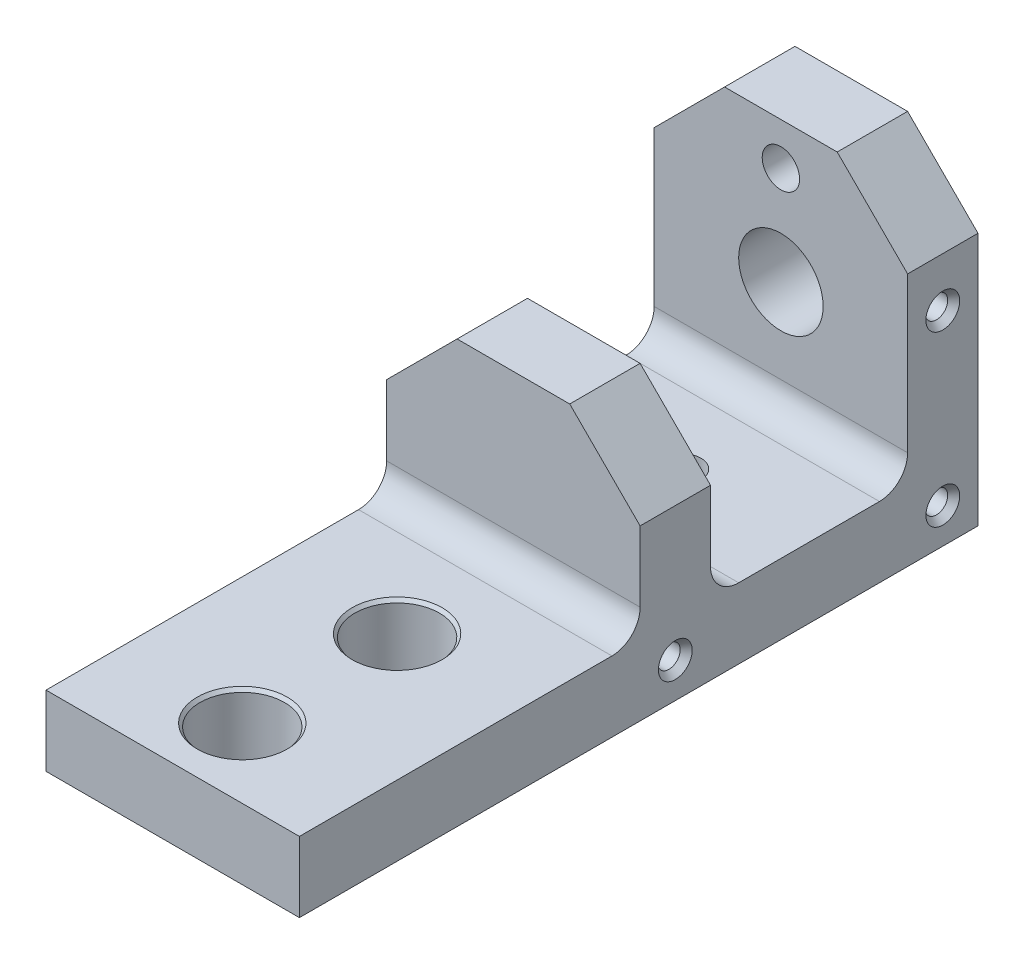
SolidWorks part; units mm, degrees
material "AISI 1018 Steel, Cold Rolled"
ref_plane "Front" through (0, 0, 0) normal (0, 0, 1) x (1, 0, 0)
ref_plane "Top" through (0, 0, 0) normal (0, 1, 0) x (1, 0, 0)
ref_plane "Right" through (0, 0, 0) normal (1, 0, 0) x (0, 0, -1)
sketch "Sketch5" plane through (0, 0, 0) normal (1, 0, 0) x (0, 0, -1)
  line L0 (0, 46.0375) -> (0, -7.9375)
  line L3 (0, -7.9375) -> (-92.71, -7.9375)
  line L4 (-92.71, -7.9375) -> (-92.71, 7.9375)
  line L5 (-92.71, 7.9375) -> (-15.875, 7.9375)
  line L6 (-15.875, 7.9375) -> (-15.875, 46.0375)
  line L7 (-15.875, 46.0375) -> (0, 46.0375)
  line L8 (-92.71, 0) -> (0, 0) construction
  dimension "D1" = 15.875
  dimension "D2" = 76.835
  dimension "D3" = 38.1
extrude "Extrude4" add sketch "Sketch5" along normal blind 57.15
sketch "Sketch9" plane through (57.15, 0, 0) normal (1, 0, 0) x (0, 0, -1)
  line L0 (0, 7.9375) -> (44.45, 7.9375)
  line L1 (44.45, 7.9375) -> (44.45, 65.0875)
  line L2 (44.45, 65.0875) -> (60.325, 65.0875)
  line L3 (60.325, 65.0875) -> (60.325, -7.9375)
  line L4 (60.325, -7.9375) -> (0, -7.9375)
  line L5 (0, -7.9375) -> (0, 46.0375) construction
  line L6 (0, -7.9375) -> (0, 7.9375)
  line L9 (0, 46.0375) -> (-15.875, 46.0375) construction
  line L10 (0, -7.9375) -> (0, 46.0375) construction
  line L12 (-92.71, 7.9375) -> (-92.71, -7.9375) construction
  dimension "D1" = 44.45
  dimension "D2" = 73.025
extrude "Extrude7" add sketch "Sketch9" against normal up to surface (57.15 mm away)
sketch "Sketch10" plane through (0, 0, -60.325) normal (0, 0, -1) x (-1, 0, 0)
  line L0 (-28.575, 33.3375) -> (-28.575, 7.9375) construction
  line L1 (0, 7.9375) -> (-57.15, 7.9375) construction
  circle A0 centre (-28.575, 33.3375) radius 9.525
  dimension "D2" = 19.05
  dimension "D1" = 25.4
extrude "Cut-Extrude2" cut sketch "Sketch10" against normal up to next
hole_wizard "3/8-24 Tapped Hole1" positions "Sketch12" profile "Sketch11" tap size "3/8-24" standard "Ansi Inch"
sketch "Sketch12" plane through (0, 0, -60.325) normal (0, 0, -1) x (-1, 0, 0)
  line L0 (-28.575, 55.5625) -> (-28.575, 33.3375) construction
  circle A0 centre (-28.575, 33.3375) radius 9.525 construction
  point P0 (-28.575, 55.5625)
  dimension "D1" = 22.225
cosmetic thread "Hole Thread1" parameters "D2"=9.525
sketch "Sketch11" plane through (28.575, 55.5625, -60.325) normal (1, 0, 0) x (0, 1, 0)
  line L0 (0, 0) -> (0, 15.875)
  line L1 (0, 15.875) -> (4.2164, 15.875)
  line L2 (4.2164, 15.875) -> (4.2164, 1.3587)
  line L3 (4.2164, 1.3587) -> (5.3975, 0)
  line L5 (5.3975, 0) -> (0, 0)
  line L6 (-4.2164, 1.3587) -> (-5.3975, 0) construction
  line L11 (0, -6.35) -> (0, 107.95) construction
  dimension "Thru Tap Drill Dia." = 8.4328
  dimension "Thru Tap Drill Depth" = 15.875
  dimension "Near C'Sink Dia." = 10.795
  dimension "Near C'Sink Angle" = 82
hole_wizard "3/8-24 Tapped Hole2" positions "Sketch14" profile "Sketch13" tap size "3/8-24" standard "Ansi Inch"
sketch "Sketch14" plane through (0, -7.9375, 0) normal (0, -1, 0) x (1, 0, 0)
  line L0 (28.575, 0) -> (28.575, -22.225) construction
  line L1 (0, 0) -> (57.15, 0) construction
  point P0 (28.575, -22.225)
  dimension "D1" = 22.225
cosmetic thread "Hole Thread2" parameters "D2"=9.525
sketch "Sketch13" plane through (28.575, -7.9375, -22.225) normal (1, 0, 0) x (0, 0, -1)
  line L0 (0, 0) -> (0, 15.875)
  line L1 (0, 15.875) -> (4.2164, 15.875)
  line L2 (4.2164, 15.875) -> (4.2164, 1.3587)
  line L3 (4.2164, 1.3587) -> (5.3975, 0)
  line L5 (5.3975, 0) -> (0, 0)
  line L6 (-4.2164, 1.3587) -> (-5.3975, 0) construction
  line L11 (0, -6.35) -> (0, 107.95) construction
  dimension "Thru Tap Drill Dia." = 8.4328
  dimension "Thru Tap Drill Depth" = 15.875
  dimension "Near C'Sink Dia." = 10.795
  dimension "Near C'Sink Angle" = 82
hole_wizard "1/4-20 Tapped Hole1" positions "Sketch16" profile "Sketch15" tap size "1/4-20" standard "Ansi Inch"
sketch "Sketch16" plane through (0, 0, 0) normal (-1, 0, 0) x (0, 0, 1)
  line L0 (-52.3875, 38.1) -> (-52.3875, 0) construction
  line L1 (-52.3875, 0) -> (7.9375, 0) construction
  line L2 (7.9375, 0) -> (7.9375, 7.9375) construction
  line L5 (-60.325, 38.1) -> (-44.45, 38.1) construction
  line L6 (-60.325, 65.0875) -> (-60.325, -7.9375) construction
  line L10 (0, 7.9375) -> (15.875, 7.9375) construction
  line L11 (0, 7.9375) -> (0, 46.0375) construction
  line L12 (15.875, 46.0375) -> (15.875, 7.9375) construction
  line L15 (-33.0172, 7.9375) -> (-33.0172, 0) construction
  line L16 (0, 7.9375) -> (-44.45, 7.9375) construction
  line L17 (-33.0172, 0) -> (-33.0172, -7.9375) construction
  line L18 (92.71, -7.9375) -> (-60.325, -7.9375) construction
  line L21 (-44.45, 7.9375) -> (-44.45, 65.0875) construction
  point P0 (-52.3875, 0)
  point P1 (7.9375, 0)
  point P3 (-52.3875, 38.1)
  dimension "D1" = 38.1
sketch "Sketch15" plane through (0, 0, -52.3875) normal (0, 1, 0) x (0, 0, 1)
  line L0 (0, 0) -> (0, 18.0438)
  line L1 (0, 18.0438) -> (2.5527, 16.51)
  line L2 (2.5527, 16.51) -> (2.5527, 1.4464)
  line L3 (2.5527, 1.4464) -> (3.81, 0)
  line L5 (3.81, 0) -> (0, 0)
  line L6 (-2.5527, 1.4464) -> (-3.81, 0) construction
  line L10 (0, 18.0438) -> (-2.5527, 16.51) construction
  line L11 (0, -6.35) -> (0, 107.95) construction
  dimension "Tap Drill Dia." = 5.1054
  dimension "Tap Drill Depth" = 16.51
  dimension "Near C'Sink Dia." = 7.62
  dimension "Near C'Sink Angle" = 82
  dimension "Drill Angle" = 118
cosmetic thread "Hole Thread3" parameters "D1"=12.7, "D2"=6.35
cosmetic thread "Hole Thread4" parameters "D1"=12.7, "D2"=6.35
cosmetic thread "Hole Thread5" parameters "D1"=12.7, "D2"=6.35
hole_wizard "1/4-20 Tapped Hole2" positions "Sketch18" profile "Sketch17" tap size "1/4-20" standard "Ansi Inch"
sketch "Sketch18" plane through (57.15, 0, 0) normal (1, 0, 0) x (0, 0, -1)
  line L1 (60.325, 38.1) -> (44.45, 38.1) construction
  point P0 (52.3875, 0)
  point P5 (-7.9375, 0)
  point P8 (52.3875, 38.1)
sketch "Sketch17" plane through (57.15, 0, -52.3875) normal (0, 1, 0) x (0, 0, -1)
  line L0 (0, 0) -> (0, 18.0438)
  line L1 (0, 18.0438) -> (2.5527, 16.51)
  line L2 (2.5527, 16.51) -> (2.5527, 1.4464)
  line L3 (2.5527, 1.4464) -> (3.81, 0)
  line L5 (3.81, 0) -> (0, 0)
  line L6 (-2.5527, 1.4464) -> (-3.81, 0) construction
  line L10 (0, 18.0438) -> (-2.5527, 16.51) construction
  line L11 (0, -6.35) -> (0, 107.95) construction
  dimension "Tap Drill Dia." = 5.1054
  dimension "Tap Drill Depth" = 16.51
  dimension "Near C'Sink Dia." = 7.62
  dimension "Near C'Sink Angle" = 82
  dimension "Drill Angle" = 118
cosmetic thread "Hole Thread7" parameters "D1"=25.4, "D2"=6.35
cosmetic thread "Hole Thread8" parameters "D1"=25.4, "D2"=6.35
cosmetic thread "Hole Thread9" parameters "D1"=25.4, "D2"=6.35
sketch "Sketch19" plane through (0, 0, -60.325) normal (0, 0, -1) x (-1, 0, 0)
  line L0 (-57.15, 49.2125) -> (-41.275, 65.0875)
  line L1 (-57.15, -7.9375) -> (-57.15, 65.0875) construction
  line L2 (0, 65.0875) -> (-57.15, 65.0875) construction
  line L3 (-41.275, 65.0875) -> (-57.15, 65.0875)
  line L4 (-57.15, 65.0875) -> (-57.15, 49.2125)
  line L5 (0, 49.2125) -> (0, 65.0875)
  line L6 (0, 65.0875) -> (0, -7.9375) construction
  line L7 (0, 65.0875) -> (-15.875, 65.0875)
  line L8 (-15.875, 65.0875) -> (0, 49.2125)
  dimension "D1" = 15.875
extrude "Cut-Extrude3" cut sketch "Sketch19" against normal up to surface (15.875 mm away)
hole_wizard "1/2 Clearance Hole1" positions "Sketch23" profile "Sketch22" hole size "1/2" standard "Ansi Inch"
sketch "Sketch23" plane through (0, -7.9375, 0) normal (0, -1, 0) x (1, 0, 0)
  line L0 (28.575, 42.1005) -> (28.575, 77.0255) construction
  line L3 (28.575, 77.0255) -> (28.575, 92.71) construction
  line L5 (57.15, 92.71) -> (0, 92.71) construction
  point P0 (28.575, 77.0255)
  point P1 (28.575, 42.1005)
  dimension "D1" = 34.925
  dimension "D2" = 15.6845
sketch "Sketch22" plane through (28.575, -7.9375, 77.0255) normal (1, 0, 0) x (0, 0, -1)
  line L0 (0, 0) -> (0, 15.875)
  line L1 (0, 15.875) -> (10.16, 15.875)
  line L2 (9.525, 15.1445) -> (9.525, 0.7305)
  line L3 (9.525, 0.7305) -> (10.16, 0)
  line L5 (10.16, 0) -> (0, 0)
  line L6 (-9.525, 0.7305) -> (-10.16, 0) construction
  line L7 (10.16, 15.875) -> (9.525, 15.1445)
  line L8 (-10.16, 15.875) -> (-9.525, 15.1445) construction
  line L11 (0, -6.35) -> (0, 107.95) construction
  dimension "Thru Hole Dia." = 19.05
  dimension "Thru Hole Depth" = 15.875
  dimension "Near C'Sink Dia." = 20.32
  dimension "Near C'Sink Angle" = 82
  dimension "Far C'Sink Dia." = 20.32
  dimension "Far C'Sink Angle" = 82
sketch "Sketch24" plane through (0, 0, 15.875) normal (0, 0, 1) x (1, 0, 0)
  line L0 (0, 30.1625) -> (15.875, 46.0375)
  line L1 (0, 46.0375) -> (0, 7.9375) construction
  line L2 (57.15, 46.0375) -> (0, 46.0375) construction
  line L3 (15.875, 46.0375) -> (0, 46.0375)
  line L4 (0, 46.0375) -> (0, 30.1625)
  line L5 (57.15, 30.1625) -> (57.15, 46.0375)
  line L6 (57.15, 46.0375) -> (57.15, 7.9375) construction
  line L7 (57.15, 46.0375) -> (41.275, 46.0375)
  line L8 (41.275, 46.0375) -> (57.15, 30.1625)
extrude "Cut-Extrude4" cut sketch "Sketch24" against normal up to next
fillet "Fillet4" radius 6.35
